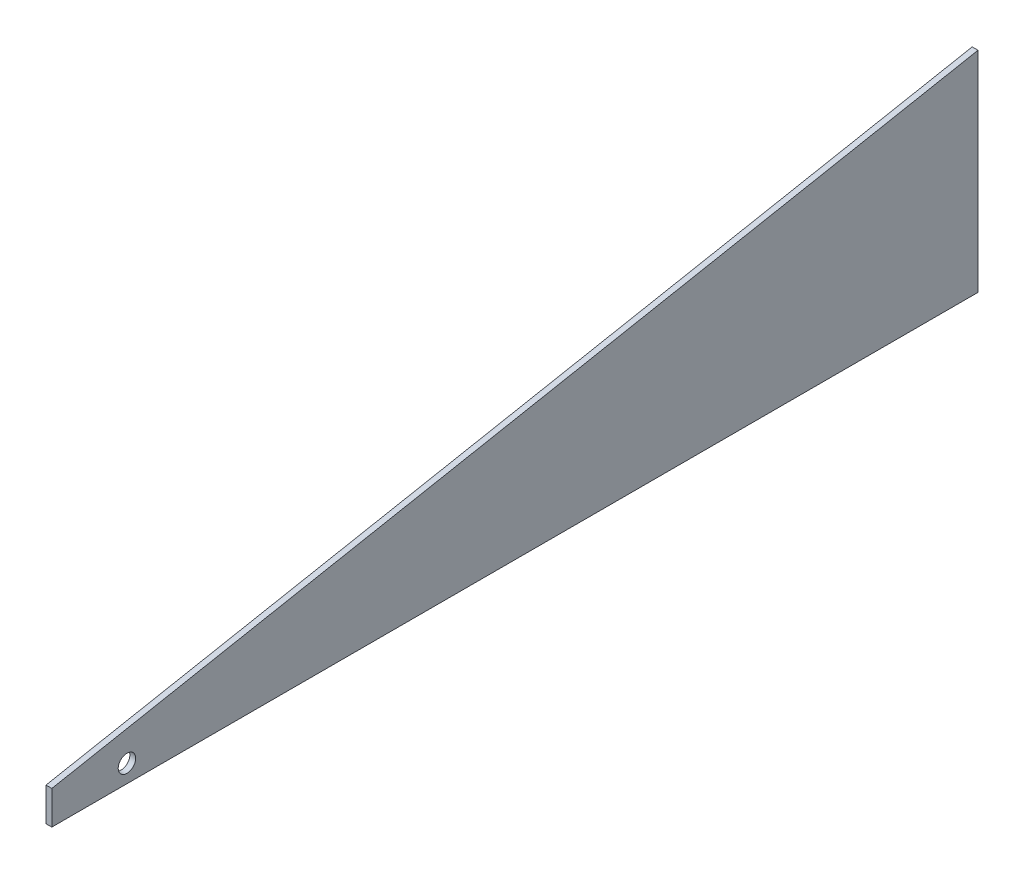
SolidWorks part; units mm, degrees
material "AISI 1020"
ref_plane "Plano frontal" through (0, 0, 0) normal (0, 0, 1) x (1, 0, 0)
ref_plane "Plano superior" through (0, 0, 0) normal (0, 1, 0) x (1, 0, 0)
ref_plane "Plano direito" through (0, 0, 0) normal (1, 0, 0) x (0, 0, -1)
sketch "Esboço1" plane through (0, 0, 0) normal (1, 0, 0) x (0, 0, -1)
  line L2 (-131, -26) -> (-131, -37.5)
  line L3 (-131, -37.5) -> (187, -37.5)
  line L6 (-131, -26) -> (187, 34.5)
  line L7 (187, -37.5) -> (187, 34.5)
  point P0 (0, 0)
  dimension "D1" = 318
  dimension "D3" = 11.5
extrude "Ressalto-extrusão1" add sketch "Esboço1" along normal blind 2
hole_wizard "Broca de rosquear de cano para tarraxa de 1/810" positions "Esboço26" profile "Esboço27" hole size "1/8" standard "Ansi Inch"
sketch "Esboço26" plane through (2, 0, 0) normal (1, 0, 0) x (0, 0, -1)
  point P0 (-105.2025, -31.4203)
sketch "Esboço27" plane through (2, -31.4203, 105.2025) normal (0, 1, 0) x (0, 0, -1)
  line L0 (0, 0) -> (0, 5.8026)
  line L1 (0, 5.8026) -> (3, 4)
  line L2 (3, 4) -> (3, 0)
  line L5 (3, 0) -> (0, 0)
  line L10 (0, 5.8026) -> (-3, 4) construction
  line L11 (0, -6.35) -> (0, 107.95) construction
  dimension "Hole Dia." = 6
  dimension "Hole Depth" = 4
  dimension "Drill Angle" = 118
sketch "Esboço28" plane through (2, 0, 0) normal (1, 0, 0) x (0, 0, -1)
